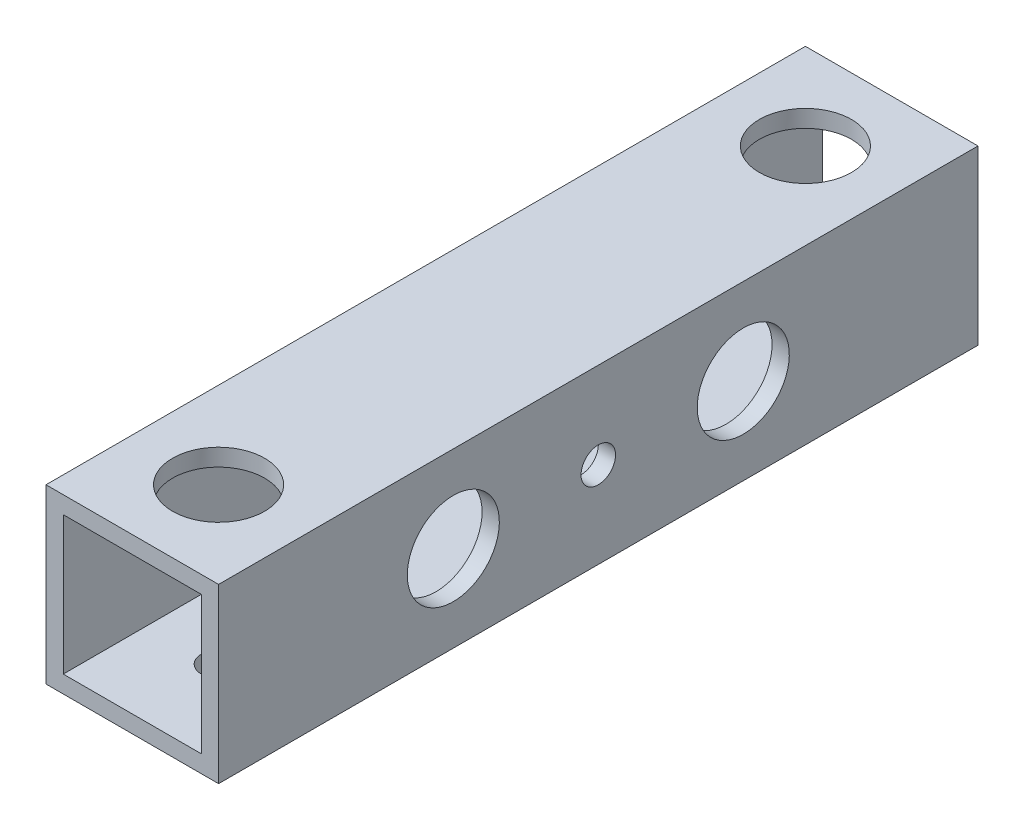
SolidWorks part; units mm, degrees
material "1060 合金"
ref_plane "正面" through (0, 0, 0) normal (0, 0, 1) x (1, 0, 0)
ref_plane "平面" through (0, 0, 0) normal (0, 1, 0) x (1, 0, 0)
ref_plane "右側面" through (0, 0, 0) normal (1, 0, 0) x (0, 0, -1)
sketch "ｽｹｯﾁ1" plane through (0, 0, 0) normal (0, 0, 1) x (1, 0, 0)
  line L1 (-7.0101, 7.7326) -> (7.9899, 7.7326)
  line L2 (-7.0101, 7.7326) -> (-7.0101, -7.2674)
  line L3 (-7.0101, -7.2674) -> (7.9899, -7.2674)
  line L4 (7.9899, 7.7326) -> (7.9899, -7.2674)
  line L9 (-5.5101, 6.2326) -> (6.4899, 6.2326)
  line L10 (-5.5101, 6.2326) -> (-5.5101, -5.7674)
  line L11 (-5.5101, -5.7674) -> (6.4899, -5.7674)
  line L12 (6.4899, 6.2326) -> (6.4899, -5.7674)
  dimension "D1" = 15
  dimension "D2" = 15
  dimension "D3" = 1.5
  dimension "D4" = 1.5
  dimension "D5" = 12
  dimension "D6" = 12
extrude "ﾎﾞｽ - 押し出し2" add sketch "ｽｹｯﾁ1" along normal blind 66
sketch "ｽｹｯﾁ3" plane through (0, 7.7326, 0) normal (0, 1, 0) x (1, 0, 0)
  line L0 (7.9899, -66) -> (-7.0101, -66) construction
  circle A0 centre (0.4899, -58.5) radius 4
  point P4 (0.4899, -66)
  dimension "D1" = 7.5
extrude "ｶｯﾄ - 押し出し1" cut sketch "ｽｹｯﾁ3" against normal blind 10
sketch "ｽｹｯﾁ4" plane through (0, 7.7326, 0) normal (0, 1, 0) x (1, 0, 0)
  line L0 (7.9899, 0) -> (-7.0101, 0) construction
  line L1 (7.9899, -66) -> (7.9899, 0) construction
  circle A0 centre (0.4899, -7.5) radius 4
  dimension "D1" = 7.5
  dimension "D2" = 7.5
extrude "ｶｯﾄ - 押し出し2" cut sketch "ｽｹｯﾁ4" against normal blind 10
sketch "ｽｹｯﾁ5" plane through (-7.0101, 0, 0) normal (-1, 0, 0) x (0, 0, 1)
  line L0 (66, 7.7326) -> (0, 7.7326) construction
  line L1 (66, -7.2674) -> (0, -7.2674) construction
  circle A0 centre (33, 0.2326) radius 4
  point P4 (0, 0)
  point P7 (33, -7.2674)
  dimension "D1" = 7.5
extrude "ｶｯﾄ - 押し出し3" cut sketch "ｽｹｯﾁ5" against normal blind 10
sketch "ｽｹｯﾁ6" plane through (7.9899, 0, 0) normal (1, 0, 0) x (0, 0, -1)
  circle A0 centre (-33, 0.2326) radius 1.5
  circle A1 centre (-33, 0.2326) radius 4 construction
  point P2 (0, 0)
extrude "ｶｯﾄ - 押し出し4" cut sketch "ｽｹｯﾁ6" against normal blind 10
sketch "ｽｹｯﾁ7" plane through (0, -7.2674, 0) normal (0, -1, 0) x (1, 0, 0)
  circle A0 centre (0.4899, 58.5) radius 1.5
  circle A1 centre (0.4899, 7.5) radius 1.5
  circle A2 centre (0.4899, 7.5) radius 4 construction
  circle A3 centre (0.4899, 58.5) radius 4 construction
  point P4 (0, 0)
  point P7 (0, 0)
extrude "ｶｯﾄ - 押し出し5" cut sketch "ｽｹｯﾁ7" against normal blind 10
sketch "ｽｹｯﾁ8" plane through (-7.0101, 0, 0) normal (-1, 0, 0) x (0, 0, 1)
  line L0 (66, 7.7326) -> (66, -7.2674) construction
  line L1 (0, 7.7326) -> (0, -7.2674) construction
  circle A0 centre (45.6, 0.2326) radius 1.5
  circle A1 centre (20.4, 0.2326) radius 1.5
  circle A2 centre (33, 0.2326) radius 4 construction
  point P6 (0, 0)
  point P9 (66, 0.2326)
  point P10 (0, 0)
  point P13 (0, 0.2326)
  dimension "D1" = 25.2
  dimension "D2" = 12.6
extrude "ｶｯﾄ - 押し出し6" cut sketch "ｽｹｯﾁ8" against normal blind 10
sketch "ｽｹｯﾁ9" plane through (7.9899, 0, 0) normal (1, 0, 0) x (0, 0, -1)
  circle A0 centre (-20.4, 0.2326) radius 4
  circle A1 centre (-45.6, 0.2326) radius 4
  circle A2 centre (-20.4, 0.2326) radius 1.5 construction
  circle A3 centre (-45.6, 0.2326) radius 1.5 construction
  point P4 (0, 0)
  point P7 (0, 0)
extrude "ｶｯﾄ - 押し出し7" cut sketch "ｽｹｯﾁ9" against normal blind 10
